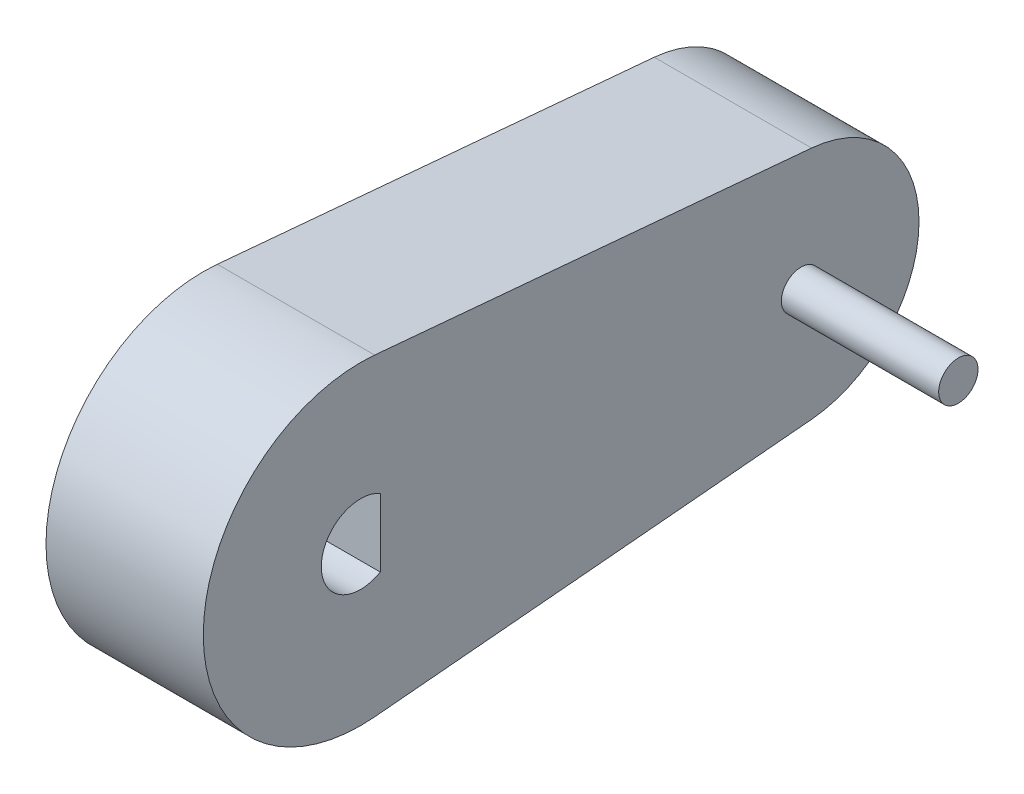
SolidWorks part; units mm, degrees
ref_plane "Front Plane" through (0, 0, 0) normal (0, 0, 1) x (1, 0, 0)
ref_plane "Top Plane" through (0, 0, 0) normal (0, 1, 0) x (1, 0, 0)
ref_plane "Right Plane" through (0, 0, 0) normal (1, 0, 0) x (0, 0, -1)
sketch "Sketch1" plane through (0, 0, 0) normal (1, 0, 0) x (0, 0, -1)
  line L0 (4.5357, 50.5971) -> (145.6418, 37.9478)
  line L1 (4.5357, -50.5971) -> (145.6418, -37.9478)
  line L2 (6.35, 10.9985) -> (6.35, -10.9985)
  arc A0 (4.5357, 50.5971) -> (4.5357, -50.5971) centre (0, 0) ccw
  arc A1 (145.6418, -37.9478) -> (145.6418, 37.9478) centre (142.24, 0) ccw
  arc A2 (6.35, 10.9985) -> (6.35, -10.9985) centre (0, 0) ccw
  dimension "D1" = 101.6
  dimension "D2" = 76.2
  dimension "D4" = 25.4
  dimension "D3" = 142.24
  dimension "D5" = 19.05
extrude "Boss-Extrude1" add sketch "Sketch1" along normal blind 50.8
sketch "Sketch2" plane through (50.8, 0, 0) normal (1, 0, 0) x (0, 0, -1)
  circle A0 centre (142.24, 0) radius 6.35
  dimension "D1" = 12.7
extrude "Boss-Extrude2" add sketch "Sketch2" along normal blind 50.8
